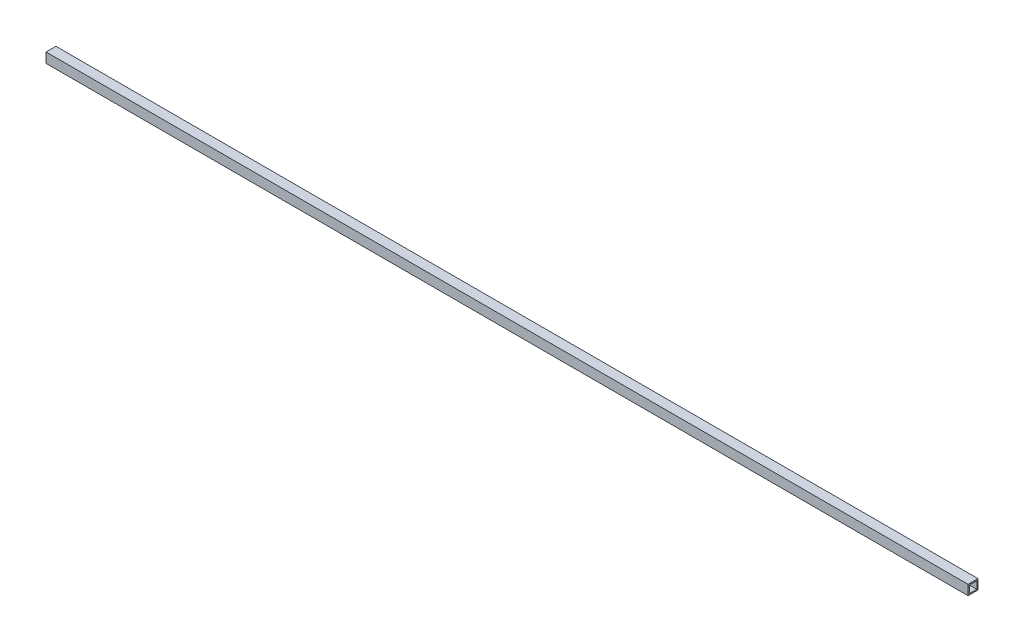
SolidWorks part; units mm, degrees
material "AISI 304"
ref_plane "Front Plane" through (0, 0, 0) normal (0, 0, 1) x (1, 0, 0)
ref_plane "Top Plane" through (0, 0, 0) normal (0, 1, 0) x (1, 0, 0)
ref_plane "Right Plane" through (0, 0, 0) normal (1, 0, 0) x (0, 0, -1)
sketch "Sketch1" plane through (0, 0, 0) normal (1, 0, 0) x (0, 0, -1)
  line L0 (-19.05, 19.05) -> (-19.05, -19.05)
  line L1 (25.4, 25.4) -> (-25.4, 25.4)
  line L2 (25.4, 25.4) -> (25.4, -25.4)
  line L3 (25.4, -25.4) -> (-25.4, -25.4)
  line L4 (-25.4, 25.4) -> (-25.4, -25.4)
  line L5 (25.4, 25.4) -> (-25.4, -25.4) construction
  line L6 (25.4, -25.4) -> (-25.4, 25.4) construction
  line L7 (19.05, -19.05) -> (-19.05, -19.05)
  line L8 (19.05, 19.05) -> (19.05, -19.05)
  line L9 (19.05, 19.05) -> (-19.05, 19.05)
  point P0 (0, 0)
  dimension "D1" = 50.8
  dimension "D2" = 50.8
  dimension "D3" = 6.35
extrude "Boss-Extrude1" add sketch "Sketch1" along normal up to surface (4736.465 mm away)
equation "\"D2@Sketch1\"=\"bracing_h\""
equation "\"D1@Sketch1\"=\"bracing_w\""
equation "\"bracing_w\"= 2in"
equation "\"bracing_h\"= 2in"
equation "\"bracing_t\"= 0.25in"
equation "\"D3@Sketch1\"=\"bracing_t\""
